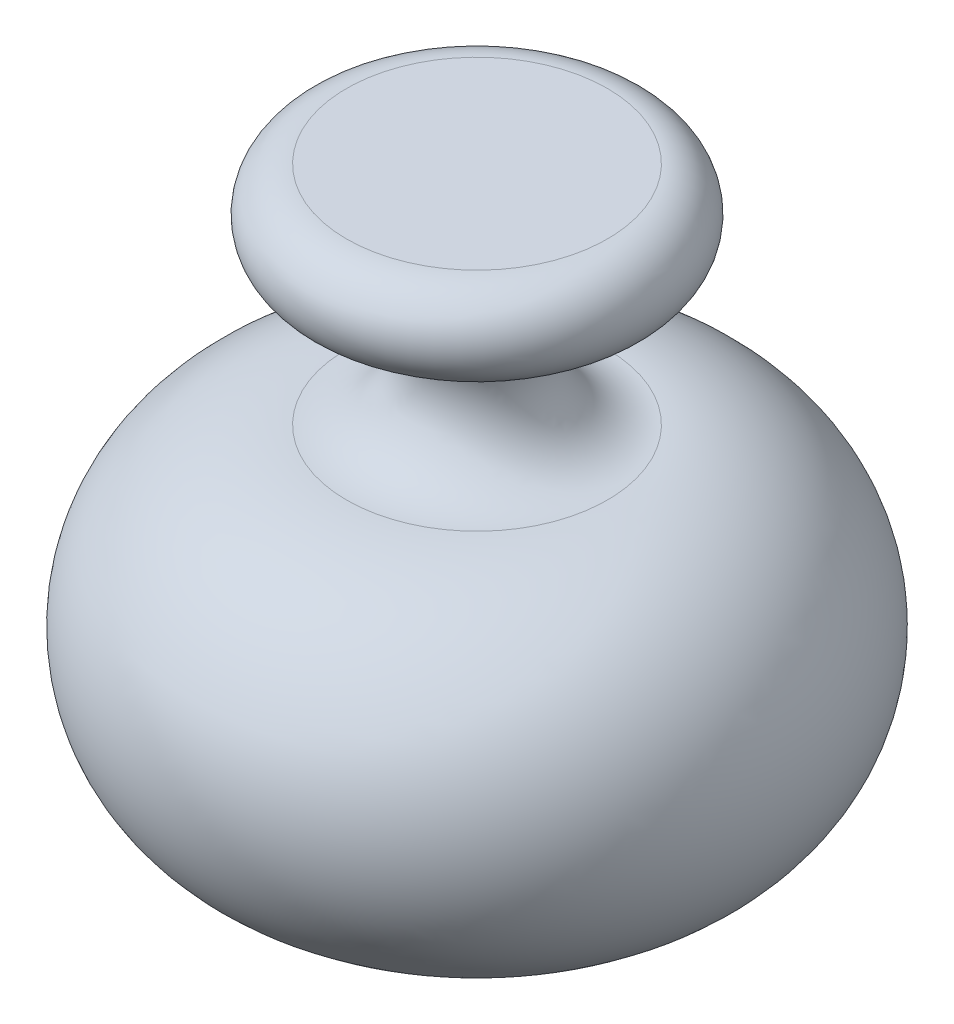
SolidWorks part; units mm, degrees
ref_plane "Přední rovina" through (0, 0, 0) normal (0, 0, 1) x (1, 0, 0)
ref_plane "Vrchní rovina" through (0, 0, 0) normal (0, 1, 0) x (1, 0, 0)
ref_plane "Pravá rovina" through (0, 0, 0) normal (1, 0, 0) x (0, 0, -1)
sketch "Skica1" plane through (0, 0, 0) normal (0, 0, 1) x (1, 0, 0)
  line L0 (0, 66) -> (0, -5.1662) construction
  line L1 (0, 0) -> (15, 0)
  line L2 (15, 66) -> (0, 66)
  line L3 (0, 66) -> (0, 0)
  arc A0 (15, 0) -> (15, 40) centre (15, 20) ccw
  arc A1 (15, 40) -> (15, 56) centre (15, 48) cw
  arc A2 (15, 56) -> (15, 66) centre (15, 61) ccw
  point P11 (0, 0)
  point P12 (0, 0)
  point P13 (0, 0)
  point P14 (0, 0)
  point P15 (0, -5.1662)
  dimension "D1" = 20
  dimension "D2" = 8
  dimension "D3" = 5
  dimension "D4" = 15
revolve "Rotovat1" add sketch "Skica1" angle 360 about L0
